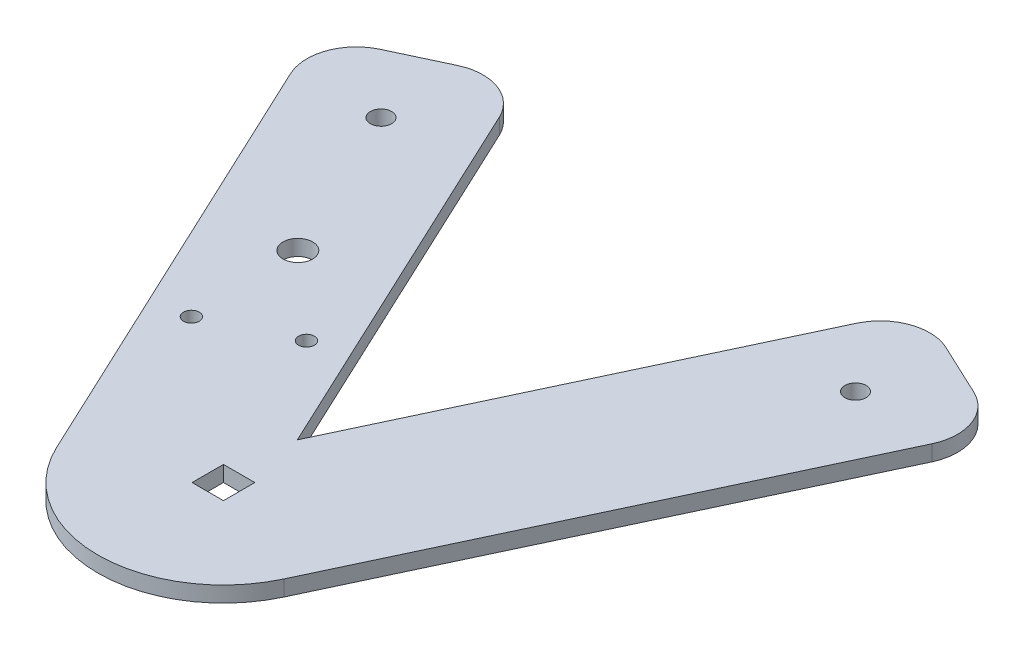
SolidWorks part; units mm, degrees
ref_plane "Front Plane" through (0, 0, 0) normal (0, 0, 1) x (1, 0, 0)
ref_plane "Top Plane" through (0, 0, 0) normal (0, 1, 0) x (1, 0, 0)
ref_plane "Right Plane" through (0, 0, 0) normal (1, 0, 0) x (0, 0, -1)
sketch "Sketch1" plane through (0, 0, 0) normal (0, 1, 0) x (1, 0, 0)
  line L0 (-47.994, 79.8634) -> (47.994, 79.8634) construction
  line L1 (-3.175, -3.175) -> (3.175, -3.175)
  line L2 (-3.175, -3.175) -> (-3.175, 3.175)
  line L3 (-3.175, 3.175) -> (3.175, 3.175)
  line L4 (3.175, -3.175) -> (3.175, 3.175)
  line L5 (-3.175, -3.175) -> (3.175, 3.175) construction
  line L6 (-3.175, 3.175) -> (3.175, -3.175) construction
  line L7 (-69.1089, 87.4917) -> (-22.9946, -10.7893)
  line L8 (22.9946, -10.7893) -> (69.1089, 87.4917)
  line L9 (-40.3657, 100.9783) -> (0, 14.9491)
  line L10 (0, 14.9491) -> (40.3657, 100.9783)
  line L11 (40.3657, 100.9783) -> (69.1089, 87.4917)
  line L12 (-69.1089, 87.4917) -> (-40.3657, 100.9783)
  line L13 (-57.544, 100.2168) -> (-36.9754, 56.38) construction
  line L14 (-7.9939, -39.4606) -> (21230.7358, 45225.4967) construction
  line L15 (-32.2979, 25.812) -> (-16.4552, 33.2455) construction
  circle A0 centre (47.994, 79.8634) radius 2.15
  circle A1 centre (-47.994, 79.8634) radius 2.15
  arc A2 (22.9946, -10.7893) -> (-22.9946, -10.7893) centre (0, 0) cw
  circle A3 centre (-33.1269, 48.1779) radius 3
  circle A4 centre (-32.2979, 25.812) radius 1.6
  circle A5 centre (-16.4552, 33.2455) radius 1.6
  point P4 (0, 0)
  point P10 (0, 79.8634)
  point P19 (54.7373, 94.235)
  point P20 (-54.7373, 94.235)
  point P31 (-24.3765, 29.5287)
  dimension "D3" = 4.3
  dimension "D7" = 25.4
  dimension "D8" = 6
  dimension "D9" = 35
  dimension "D11" = 3.2
  dimension "D1" = 6.35
  dimension "D2" = 31.75
  dimension "D4" = 93.175
  dimension "D5" = 95.988
  dimension "D6" = 15.875
  dimension "D10" = 17.5
  dimension "D12" = 20.6
extrude "Boss-Extrude1" add sketch "Sketch1" along normal blind 3.175
fillet "Fillet1" radius 10 4 edges at (69.1089, 1.5875, -87.4917) (40.3657, 1.5875, -100.9783) (-40.3657, 1.5875, -100.9783) (-69.1089, 1.5875, -87.4917)
